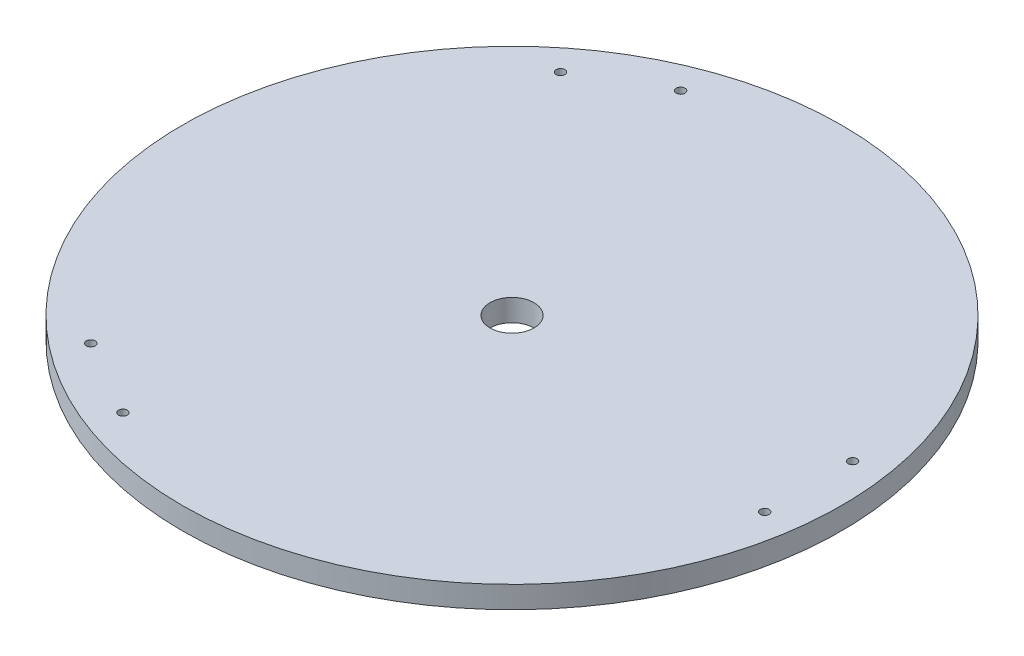
SolidWorks part; units mm, degrees
material "Acrylic"
ref_plane "Front Plane" through (0, 0, 0) normal (0, 0, 1) x (1, 0, 0)
ref_plane "Top Plane" through (0, 0, 0) normal (0, 1, 0) x (1, 0, 0)
ref_plane "Right Plane" through (0, 0, 0) normal (1, 0, 0) x (0, 0, -1)
sketch "Sketch1" plane through (0, 0, 0) normal (0, 1, 0) x (1, 0, 0)
  circle A0 centre (0, 0) radius 150
  circle A1 centre (0, 0) radius 10
  circle A2 centre (135, 20) radius 2
  circle A3 centre (135, -20) radius 2
  circle A4 centre (-50.1795, -126.9134) radius 2
  circle A5 centre (-84.8205, -106.9134) radius 2
  circle A6 centre (-84.8205, 106.9134) radius 2
  circle A7 centre (-50.1795, 126.9134) radius 2
  point P19 (0, 0)
  dimension "D1" = 300
  dimension "D2" = 20
  dimension "D3" = 4
  dimension "D4" = 135
  dimension "D5" = 20
  dimension "D6" = 20
  dimension "D7" = 3
extrude "Boss-Extrude1" add sketch "Sketch1" along normal blind 10
